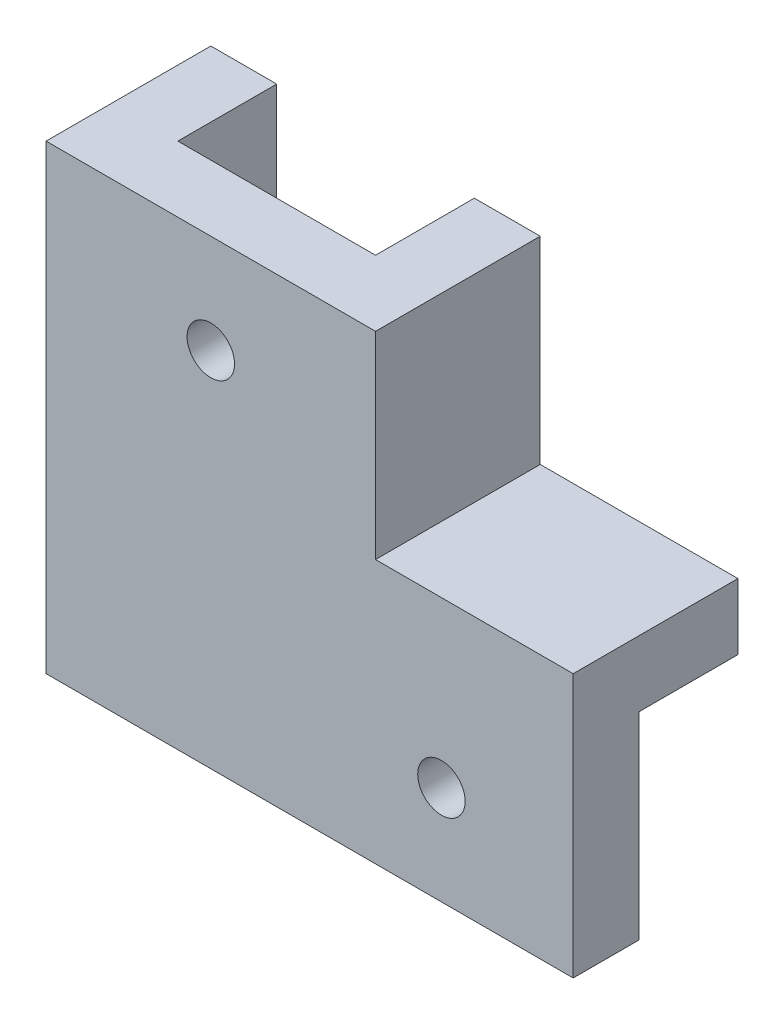
SolidWorks part; units mm, degrees
ref_plane "前视基准面" through (0, 0, 0) normal (0, 0, 1) x (1, 0, 0)
ref_plane "上视基准面" through (0, 0, 0) normal (0, 1, 0) x (1, 0, 0)
ref_plane "右视基准面" through (0, 0, 0) normal (1, 0, 0) x (0, 0, -1)
sketch "Sketch1" plane through (0, 0, 0) normal (0, 0, 1) x (1, 0, 0)
  line L0 (-7.5299, -25.8068) -> (27.4701, -25.8068)
  line L3 (-7.5299, 9.1932) -> (7.4701, 9.1932)
  line L4 (-7.5299, 9.1932) -> (-7.5299, -25.8068)
  line L6 (7.4701, 9.1932) -> (7.4701, -10.8068)
  line L7 (27.4701, -25.8068) -> (27.4701, -10.8068)
  line L8 (27.4701, -10.8068) -> (7.4701, -10.8068)
  dimension "D1" = 15
  dimension "D2" = 35
  dimension "D3" = 35
  dimension "D4" = 15
extrude "Boss-Extrude1" add sketch "Sketch1" along normal blind 5
sketch "Sketch2" plane through (0, 0, 0) normal (0, 0, -1) x (-1, 0, 0)
  line L0 (-7.4701, 9.1932) -> (-12.4701, 9.1932)
  line L1 (-12.4701, 9.1932) -> (-12.4701, -5.8068)
  line L2 (-12.4701, -5.8068) -> (-27.4701, -5.8068)
  line L3 (-27.4701, -10.8068) -> (-27.4701, -5.8068)
  line L4 (-27.4701, -10.8068) -> (-7.4701, -10.8068)
  line L5 (-7.4701, -10.8068) -> (-7.4701, 9.1932)
  dimension "D1" = 5
  dimension "D2" = 5
extrude "Boss-Extrude2" add sketch "Sketch2" along normal blind 7.5 separate body
sketch "Sketch3" plane through (0, 0, 0) normal (0, 0, -1) x (-1, 0, 0)
  line L0 (7.5299, 9.1932) -> (12.5299, 9.1932)
  line L1 (7.5299, -25.8068) -> (12.5299, -25.8068)
  line L2 (12.5299, -25.8068) -> (12.5299, 9.1932)
  line L3 (7.5299, -25.8068) -> (7.5299, 9.1932)
  dimension "D1" = 5
extrude "Boss-Extrude3" add sketch "Sketch3" along normal blind 7.5 separate body
sketch "Sketch4" plane through (0, 0, 0) normal (0, 0, 1) x (1, 0, 0)
  line L1 (-12.5299, 9.1932) -> (-7.5299, 9.1932)
  line L2 (-12.5299, 9.1932) -> (-12.5299, -25.8068)
  line L3 (-12.5299, -25.8068) -> (-7.5299, -25.8068)
  line L4 (-7.5299, 9.1932) -> (-7.5299, -25.8068)
extrude "Boss-Extrude4" add sketch "Sketch4" along normal blind 5
sketch "Sketch5" plane through (0, 0, 0) normal (0, 0, 1) x (1, 0, 0)
  line L0 (7.4701, 9.1932) -> (7.4701, -10.8068)
  line L1 (7.4701, -10.8068) -> (27.4701, -10.8068)
  line L2 (27.4701, -10.8068) -> (27.4701, -5.8068)
  line L3 (27.4701, -5.8068) -> (12.4701, -5.8068)
  line L4 (12.4701, -5.8068) -> (12.4701, 9.1932)
  line L5 (12.4701, 9.1932) -> (7.4701, 9.1932)
extrude "Boss-Extrude5" add sketch "Sketch5" along normal blind 5
sketch "Sketch7" plane through (0, 0, 0) normal (0, 0, -1) x (-1, 0, 0)
  line L0 (-27.4701, -25.8068) -> (-27.4701, -10.8068) construction
  line L1 (-27.4701, -10.8068) -> (-7.4701, -10.8068) construction
  line L2 (-7.4701, 9.1932) -> (7.5299, 9.1932) construction
  line L3 (7.5299, 9.1932) -> (7.5299, -25.8068) construction
  circle A0 centre (0.0299, 1.6932) radius 1.8
  circle A1 centre (-17.4701, -18.3068) radius 1.8
  dimension "D1" = 3.6
  dimension "D2" = 3.6
  dimension "D3" = 10
  dimension "D5" = 7.5
  dimension "D6" = 7.5
  dimension "D4" = 7.5
extrude "Cut-Extrude1" cut sketch "Sketch7" against normal through all
